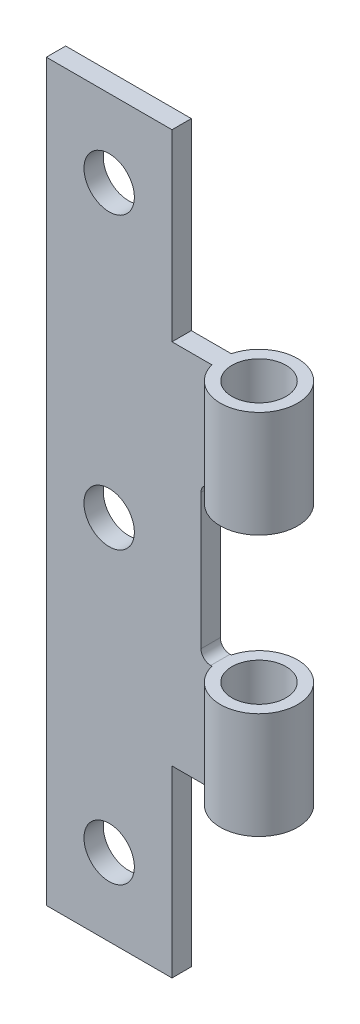
SolidWorks part; units mm, degrees
ref_plane "Front Plane" through (0, 0, 0) normal (0, 0, 1) x (1, 0, 0)
ref_plane "Top Plane" through (0, 0, 0) normal (0, 1, 0) x (1, 0, 0)
ref_plane "Right Plane" through (0, 0, 0) normal (1, 0, 0) x (0, 0, -1)
sketch "Sketch1" plane through (0, 0, 0) normal (0, 1, 0) x (1, 0, 0)
  line L1 (-1.9365, 0.5) -> (-10.5, 0.5)
  line L2 (-1.9365, -0.5) -> (-10.5, -0.5)
  line L3 (-10.5, 0.5) -> (-10.5, -0.5)
  line L4 (0, 0) -> (-1.6596, 0) construction
  line L5 (-2, 0) -> (-3.3192, 0) construction
  arc A0 (-1.9365, -0.5) -> (-1.9365, 0.5) centre (0, 0) ccw
  circle A1 centre (0, 0) radius 1.4
  dimension "D1" = 4
  dimension "D2" = 2.8
  dimension "D3" = 10.5
  dimension "D4" = 1
extrude "Boss-Extrude1" add sketch "Sketch1" along normal blind 5.5
ref_plane "Plane1" through (0, 13.5, 0) normal (0, 1, 0) x (1, 0, 0)
sketch "Sketch2" plane through (0, 13.5, 0) normal (0, 1, 0) x (1, 0, 0)
  line L0 (-1.9365, 0.5) -> (-10.5, 0.5)
  line L1 (-1.9365, -0.5) -> (-10.5, -0.5)
  line L2 (-10.5, 0.5) -> (-10.5, -0.5)
  line L3 (0, 0) -> (-5.201, 0) construction
  line L4 (-5.5414, 0) -> (-6.8605, 0) construction
  arc A0 (-1.9365, -0.5) -> (-1.9365, 0.5) centre (0, 0) ccw
  circle A1 centre (0, 0) radius 1.4
  dimension "D1" = 4
  dimension "D2" = 2.8
  dimension "D3" = 10.5
  dimension "D4" = 1
extrude "Boss-Extrude2" add sketch "Sketch2" along normal blind 5.5 separate body
sketch "Sketch3" plane through (0, 5.5, 0) normal (0, 1, 0) x (1, 0, 0)
  line L0 (-10.5, 0.5) -> (-10.5, -0.5)
  line L1 (-10.5, 0.5) -> (-2.5, 0.5)
  line L2 (-10.5, -0.5) -> (-2.5, -0.5)
  line L3 (-2.5, 0.5) -> (-2.5, -0.5)
  dimension "D1" = 8
extrude "Boss-Extrude3" add sketch "Sketch3" along normal up to next (13.5 mm away)
sketch "Sketch4" plane through (0, 19, 0) normal (0, 1, 0) x (1, 0, 0)
  line L0 (-10.5, 0.5) -> (-10.5, -0.5)
  line L1 (-10.5, 0.5) -> (-4, 0.5)
  line L2 (-10.5, -0.5) -> (-4, -0.5)
  line L3 (-4, 0.5) -> (-4, -0.5)
  dimension "D1" = 6.5
extrude "Boss-Extrude4" add sketch "Sketch4" along normal blind 9.5
sketch "Sketch5" plane through (0, 0, 0) normal (0, -1, 0) x (1, 0, 0)
  line L0 (-10.5, 0.5) -> (-10.5, -0.5)
  line L1 (-10.5, 0.5) -> (-4, 0.5)
  line L2 (-10.5, -0.5) -> (-4, -0.5)
  line L3 (-4, 0.5) -> (-4, -0.5)
  dimension "D1" = 6.5
extrude "Boss-Extrude5" add sketch "Sketch5" along normal blind 9.5
fillet "Fillet1" radius 0.5 2 edges at (-2.5, 5.5, 0) (-2.5, 13.5, 0)
sketch "Sketch6" plane through (0, 0, 0.5) normal (0, 0, 1) x (1, 0, 0)
  line L0 (-7.25, -9.5) -> (-7.25, 32.4216) construction
  line L1 (-4, -9.5) -> (-10.5, -9.5) construction
  circle A0 centre (-7.25, -5.5) radius 1.3039
  circle A1 centre (-7.25, 9.5) radius 1.3039
  circle A2 centre (-7.25, 24.5) radius 1.3039
  dimension "D1" = 4
  dimension "D2" = 3
extrude "Cut-Extrude1" cut sketch "Sketch6" against normal up to next
